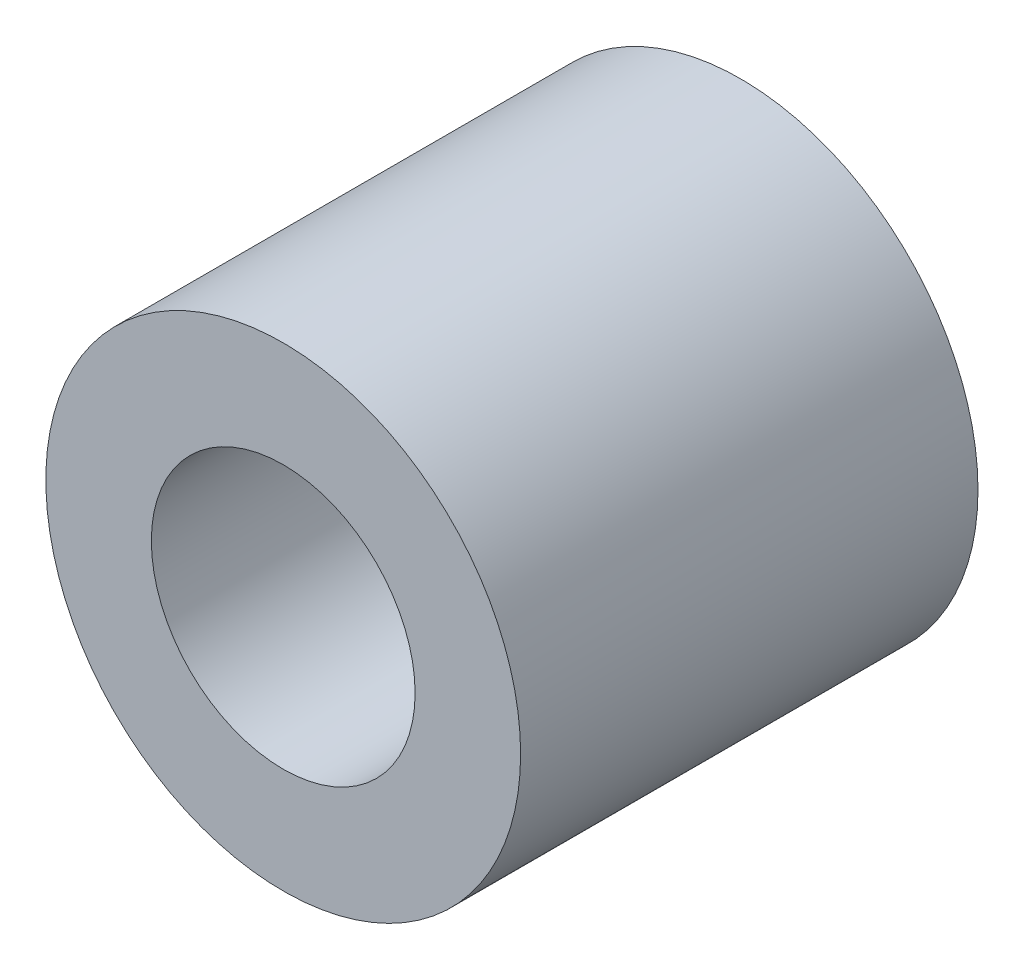
SolidWorks part; units mm, degrees
ref_plane "Front Plane" through (0, 0, 0) normal (0, 0, 1) x (1, 0, 0)
ref_plane "Top Plane" through (0, 0, 0) normal (0, 1, 0) x (1, 0, 0)
ref_plane "Right Plane" through (0, 0, 0) normal (1, 0, 0) x (0, 0, -1)
sketch "Sketch1" plane through (0, 0, 0) normal (0, 0, 1) x (1, 0, 0)
  circle A0 centre (0, 0) radius 2.5
  circle A1 centre (0, 0) radius 4.5
  dimension "D1" = 9
  dimension "D2" = 5
extrude "Boss-Extrude1" add sketch "Sketch1" along normal blind 8.67
